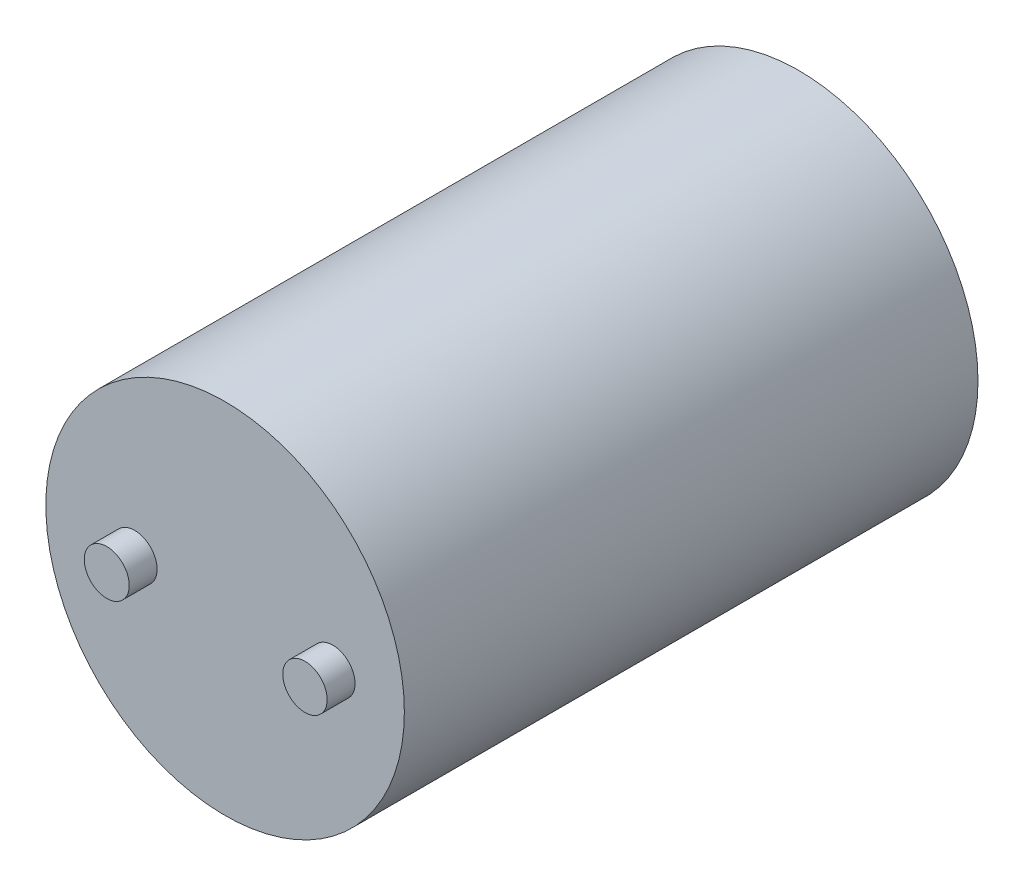
SolidWorks part; units mm, degrees
ref_plane "Front Plane" through (0, 0, 0) normal (0, 0, 1) x (1, 0, 0)
ref_plane "Top Plane" through (0, 0, 0) normal (0, 1, 0) x (1, 0, 0)
ref_plane "Right Plane" through (0, 0, 0) normal (1, 0, 0) x (0, 0, -1)
sketch "Sketch1" plane through (0, 0, 0) normal (0, 0, 1) x (1, 0, 0)
  circle A0 centre (0, 0) radius 45
  dimension "D1" = 90
extrude "Boss-Extrude1" add sketch "Sketch1" along normal blind 144
sketch "Sketch2" plane through (0, 0, 144) normal (0, 0, 1) x (1, 0, 0)
  circle A0 centre (-22.71, 0) radius 5.6451
  circle A1 centre (27.0482, 0) radius 5.573
extrude "Boss-Extrude2" add sketch "Sketch2" along normal blind 7
